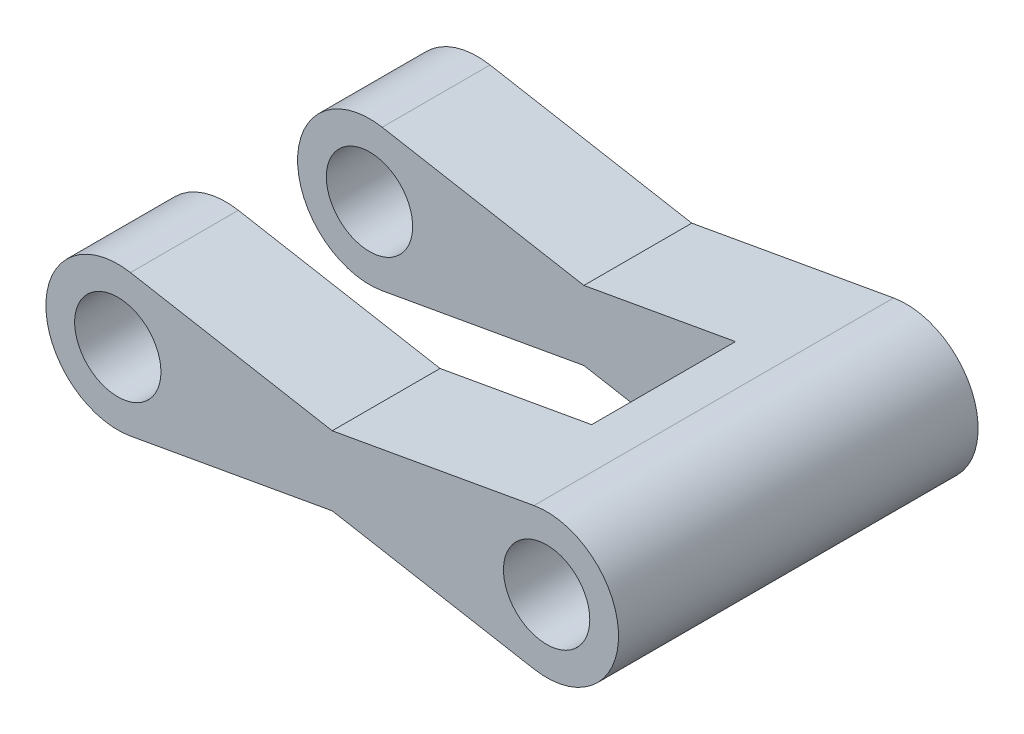
SolidWorks part; units mm, degrees
ref_plane "Front Plane" through (0, 0, 0) normal (0, 0, 1) x (1, 0, 0)
ref_plane "Top Plane" through (0, 0, 0) normal (0, 1, 0) x (1, 0, 0)
ref_plane "Right Plane" through (0, 0, 0) normal (1, 0, 0) x (0, 0, -1)
sketch "Sketch1" plane through (0, 0, 0) normal (0, 0, 1) x (1, 0, 0)
  line L0 (-149.0663, 50.7944) -> (0, 24.1174)
  line L1 (0, 24.1174) -> (149.0663, 50.7944)
  line L2 (0, 24.1174) -> (0, 0) construction
  line L3 (0, 0) -> (0, -24.1174) construction
  line L4 (-149.0663, -50.7944) -> (0, -24.1174)
  line L5 (0, -24.1174) -> (149.0663, -50.7944)
  line L6 (-149.0663, 0) -> (0, 0) construction
  line L7 (0, 0) -> (149.0663, 0) construction
  circle A0 centre (-149.0663, 0) radius 50
  circle A1 centre (149.0663, 0) radius 50
  circle A2 centre (-149.0663, 0) radius 30
  circle A3 centre (149.0663, 0) radius 30
  dimension "D1" = 100
extrude "Boss-Extrude1" add sketch "Sketch1" along normal blind 250 contours A0 A2 | A1 L1 L0 A0 L4 L5 | A1 A3
sketch "Sketch2" plane through (0, 0, 0) normal (0, 1, 0) x (1, 0, 0)
  line L0 (-199.0663, -75) -> (105.3634, -75)
  line L1 (-199.0663, 0) -> (-199.0663, -250) construction
  line L2 (105.3634, -75) -> (105.3634, -125)
  line L3 (105.3634, -175) -> (-199.0663, -175)
  line L4 (-199.0663, 0) -> (-199.0663, -250) construction
  line L5 (-199.0663, -125) -> (132.0058, -125) construction
  line L6 (-199.0663, -75) -> (-199.0663, -175)
  line L7 (105.3634, -125) -> (105.3634, -175)
  dimension "D1" = 75
extrude "Cut-Extrude1" cut sketch "Sketch2" against normal mid plane 250
sketch "Sketch3" plane through (0, 0, 250) normal (0, 0, 1) x (1, 0, 0)
  circle A0 centre (-149.0663, 0) radius 30
